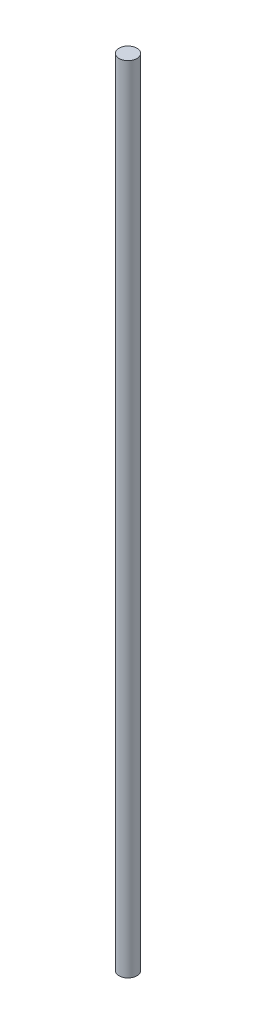
SolidWorks part; units mm, degrees
ref_plane "Front" through (0, 0, 0) normal (0, 0, 1) x (1, 0, 0)
ref_plane "Top" through (0, 0, 0) normal (0, 1, 0) x (1, 0, 0)
ref_plane "Right" through (0, 0, 0) normal (1, 0, 0) x (0, 0, -1)
sketch "Sketch1" plane through (0, 0, 0) normal (0, 1, 0) x (1, 0, 0)
  circle A0 centre (0, 0) radius 3.05
  dimension "D1" = 6.1
extrude "Boss-Extrude1" add sketch "Sketch1" along normal blind 270
